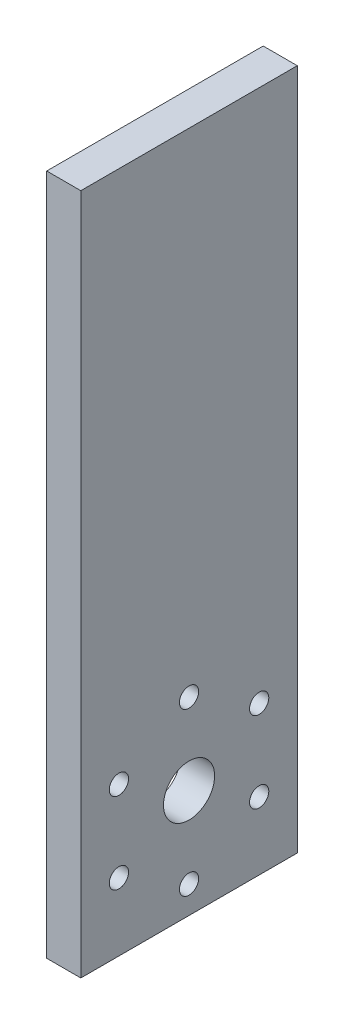
SolidWorks part; units mm, degrees
ref_plane "Front Plane" through (0, 0, 0) normal (0, 0, 1) x (1, 0, 0)
ref_plane "Top Plane" through (0, 0, 0) normal (0, 1, 0) x (1, 0, 0)
ref_plane "Right Plane" through (0, 0, 0) normal (1, 0, 0) x (0, 0, -1)
sketch "Sketch2" plane through (0, 0, 0) normal (0, 1, 0) x (1, 0, 0)
  line L1 (0, 0) -> (4, 0)
  line L2 (0, 0) -> (0, -25.4)
  line L3 (0, -25.4) -> (4, -25.4)
  line L4 (4, 0) -> (4, -25.4)
  dimension "D1" = 25.4
  dimension "D2" = 4
extrude "Boss-Extrude1" add sketch "Sketch2" along normal blind 80
sketch "Sketch3" plane through (4, 0, 0) normal (1, 0, 0) x (0, 0, -1)
  line L0 (-12.7, 0) -> (-12.7, 12.7) construction
  line L1 (-25.4, 0) -> (0, 0) construction
  circle A0 centre (-12.7, 12.7) radius 9.5
  circle A1 centre (-12.7, 22.2) radius 1.4
  circle A2 centre (-4.4728, 17.45) radius 1.4
  circle A3 centre (-4.4728, 7.95) radius 1.4
  circle A4 centre (-12.7, 3.2) radius 1.4
  circle A5 centre (-20.9272, 7.95) radius 1.4
  circle A6 centre (-20.9272, 17.45) radius 1.4
  point P20 (-12.7, 12.7)
  dimension "D2" = 19
  dimension "D3" = 2.8
  dimension "D1" = 12.7
  dimension "D4" = 6
hole_wizard "#4-40 Tapped Hole1" positions "Sketch5" profile "Sketch4" tap size "#4-40" standard "ANSI Inch"
sketch "Sketch5" plane through (4, 0, 0) normal (1, 0, 0) x (0, 0, -1)
  point P0 (-12.7, 22.2)
  point P3 (-4.4728, 17.45)
  point P6 (-4.4728, 7.95)
  point P9 (-12.7, 3.2)
  point P12 (-20.9272, 7.95)
  point P15 (-20.9272, 17.45)
sketch "Sketch4" plane through (4, 22.2, 12.7) normal (0, 1, 0) x (0, 0, -1)
  line L0 (0, 0) -> (0, 8.2792)
  line L1 (0, 8.2792) -> (1.1303, 7.6)
  line L2 (1.1303, 7.6) -> (1.1303, 0)
  line L5 (1.1303, 0) -> (0, 0)
  line L10 (0, 8.2792) -> (-1.1303, 7.6) construction
  line L11 (0, -6.35) -> (0, 107.95) construction
  dimension "Tap Drill Dia." = 2.2606
  dimension "Tap Drill Depth" = 7.6
  dimension "Drill Angle" = 118
cosmetic thread "Hole Thread1"
cosmetic thread "Hole Thread2"
cosmetic thread "Hole Thread3"
cosmetic thread "Hole Thread4"
cosmetic thread "Hole Thread5"
cosmetic thread "Hole Thread6"
sketch "Sketch6" plane through (4, 0, 0) normal (1, 0, 0) x (0, 0, -1)
  circle A0 centre (-12.7, 12.7) radius 3
  dimension "D1" = 6
extrude "Cut-Extrude1" cut sketch "Sketch6" against normal blind 80
